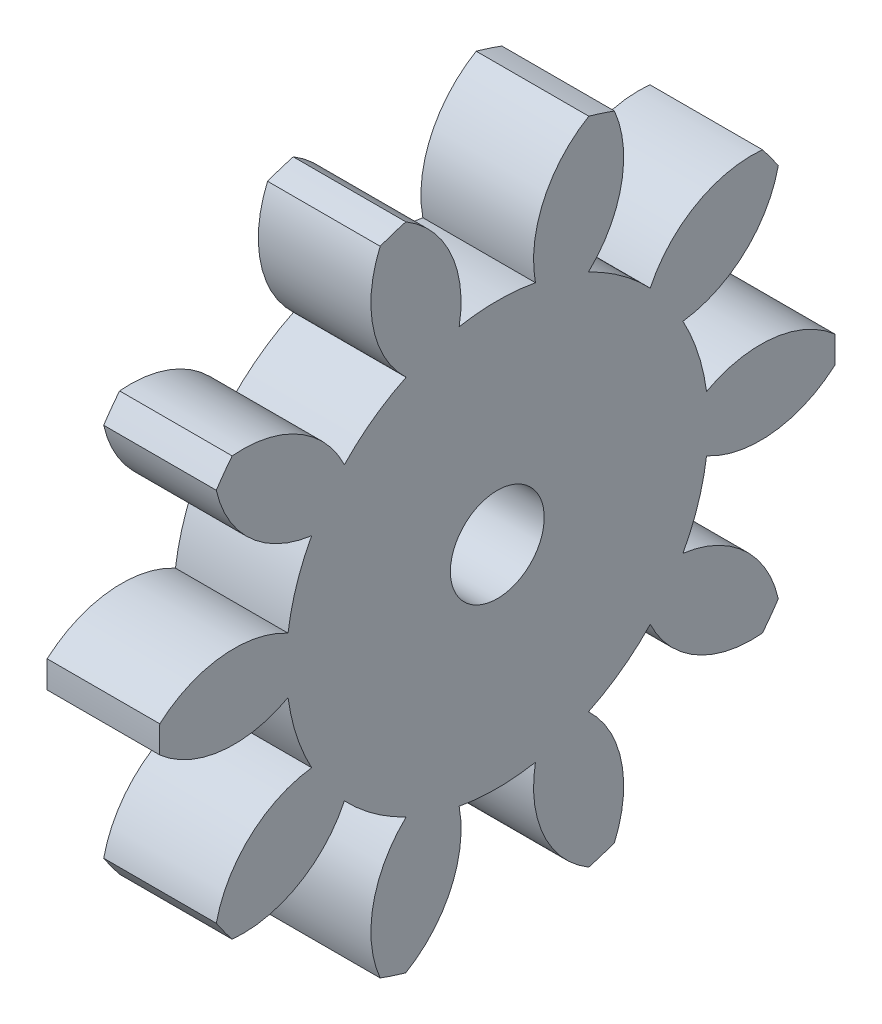
SolidWorks part; units mm, degrees
ref_plane "Plane1" through (0, 0, 0) normal (0, 0, 1) x (1, 0, 0)
ref_plane "Plane2" through (0, 0, 0) normal (0, 1, 0) x (1, 0, 0)
ref_plane "Plane3" through (0, 0, 0) normal (1, 0, 0) x (0, 0, -1)
other "Configuration Table"
sketch "HoldingSke" plane through (0, 0, 0) normal (0, 1, 0) x (1, 0, 0)
  line L0 (0, 0) -> (0.3283, -0.0579)
  line L1 (-15, 0) -> (100, 0) construction
  line L2 (0, 0) -> (-2.1039, 2.3779)
  line L3 (0, 0) -> (-11.863, 4.5341)
  line L4 (0, 0) -> (8.5048, 1.4996)
  line L5 (0, 0) -> (-46.8476, -17.4728)
  line L6 (0, 0) -> (-4.9738, -3.3558)
  line L7 (-2.1039, 2.3779) -> (8.6586, 51.2059)
  line L8 (-76.2, 54.61) -> (-75.3, 54.61)
  line L9 (-67.7845, 28.3722) -> (-49.3413, 33.142)
  line L10 (-76.2, 71.12) -> (104.1128, 71.12)
  line L11 (0, 0) -> (-6, 0)
  line L12 (-76.2, 101.6) -> (-76.093, 101.6)
  line L13 (24.9733, 27.94) -> (52.9518, 28.4284)
  line L14 (24.9733, 27.94) -> (24.9743, 27.94)
  line L15 (24.9733, 27.94) -> (100.4006, 29.5858)
  line L16 (-63.627, -3) -> (-12.827, -3)
  circle A0 centre (0, 0) radius 2.5
  circle A1 centre (0, 0) radius 11.249
  circle A2 centre (0, 0) radius 37.5
  circle A3 centre (0, 0) radius 2.5
  dimension "MHD" = 22.498
  dimension "Hub_dia" = 75
  dimension "Bore" = 5
  dimension "MBD" = 5
  dimension "Num_teeth" = 10
  dimension "Pitch" = 0.3333
  dimension "Overall_len" = 50
  dimension "Show_teeth" = 10
  dimension "Thickness" = 6
  dimension "OAL" = 50.0001
  dimension "T_dim" = 0.9
  dimension "Ap" = 14.5
  dimension "H" = 19.05
  dimension "Pitch_radius" = 180.3128
  dimension "Width" = 6
  dimension "Backlash" = 0.107
  dimension "Addendum_fac" = 1
  dimension "Dedendum_fac" = 1.25
  dimension "Clearance_fac" = 0.25
  dimension "Dedendum_add" = 0.001
  dimension "Module" = 3
sketch "BasProSke" plane through (0, 0, 0) normal (0, 1, 0) x (1, 0, 0)
  line L0 (-10, 0) -> (60, 0) construction
  line L1 (0, 0) -> (0, 18)
  line L2 (0, 0) -> (6, 0)
  line L3 (6, 0) -> (6, 18)
  line L4 (6, 18) -> (0, 18)
  dimension "Thickness" = 6
  dimension "Diameter" = 36
revolve "Base-Revolve" add sketch "BasProSke" angle 360 about L0
sketch "TooCutSke" plane through (0, 0, 0) normal (1, 0, 0) x (0, 0, -1)
  line L1 (0, 0) -> (0, 107) construction
  line L2 (0, 0) -> (-2.5334, 14.7845) construction
  line L3 (0, 0) -> (-9.174, 28.2345) construction
  line L4 (-2.5334, 14.7845) -> (-4.587, 14.1173) construction
  arc A0 (2.0333, 11.0637) -> (-2.0333, 11.0637) centre (0, 0) ccw
  arc A1 (4.9042, 17.3454) -> (-4.9042, 17.3454) centre (0, 0) ccw
  circle A2 centre (0, 0) radius 15 construction
  circle A3 centre (0, 0) radius 14.5222 construction
  arc A4 (-2.0333, 11.0637) -> (-4.9042, 17.3454) centre (-7.9314, 12.165) ccw
  arc A5 (4.9042, 17.3454) -> (2.0333, 11.0637) centre (7.9314, 12.165) ccw
  dimension "Root_dia" = 22.498
  dimension "Overcut_dia" = 36.0508
  dimension "Pitch_dia" = 30
  dimension "Base_dia" = 29.0444
  dimension "Flank_rad" = 6
  dimension "Half_ang" = 18
  dimension "Half_CT" = 2.1593
extrude "ToothCut" cut sketch "TooCutSke" along normal through all
fillet "Breaks" [suppressed] radius 0.06
fillet "RootFillets" [suppressed] radius 0.751
pattern_circular "TeethCuts" count 10 every 36 about axis through (-10, 0, 0) along (1, 0, 0) of "ToothCut", "RootFillets", "Breaks"
sketch "HubNeaOneSke" plane through (0, 0, 0) normal (-1, 0, 0) x (0, 0, 1)
  circle A0 centre (0, 0) radius 11.249
  dimension "Diameter" = 22.498
extrude "HubNearOne" [suppressed] add sketch "HubNeaOneSke" along normal blind 44.0001
sketch "HubNeaBotSke" plane through (0, 0, 0) normal (-1, 0, 0) x (0, 0, 1)
  circle A0 centre (0, 0) radius 11.249
  dimension "Diameter" = 22.498
extrude "HubNearBoth" [suppressed] add sketch "HubNeaBotSke" along normal blind 22
ref_plane "FarPln" through (6, 0, 0) normal (1, 0, 0) x (0, 0, -1)
sketch "HubFarSke" plane through (6, 0, 0) normal (1, 0, 0) x (0, 0, -1)
  circle A0 centre (0, 0) radius 11.249
  dimension "Diameter" = 22.498
extrude "HubFar" [suppressed] add sketch "HubFarSke" along normal blind 22
sketch "BorSke" plane through (0, 0, 0) normal (1, 0, 0) x (0, 0, -1)
  circle A0 centre (0, 0) radius 2.5
  dimension "Diameter" = 5
extrude "Bore" cut sketch "BorSke" along normal mid plane 100.0001
sketch "KeySke" plane through (0, 0, 0) normal (1, 0, 0) x (0, 0, -1)
  line L0 (-1, 0) -> (-1, 3.4)
  line L1 (-1, 3.4) -> (1, 3.4)
  line L2 (1, 3.4) -> (1, 0)
  line L3 (0, 0) -> (0, 34) construction
  line L4 (-1, 0) -> (1, 0)
  dimension "Offset" = 3.4
  dimension "Width" = 2
extrude "Keyway" [suppressed] cut sketch "KeySke" along normal mid plane 100.0001
pattern_circular "Keyway2" [suppressed] count 2 every 90 about axis through (-10, 0, 0) along (1, 0, 0)
equation "' \"Module@HoldingSke\" = 6.35"
equation "' \"Num_teeth@HoldingSke\" = 12"
equation "' \"Ap@HoldingSke\" =  20"
equation "' \"Ap@HoldingSke\" = 20"
equation "' \"Width@HoldingSke\" = 0.5 * 25.4"
equation "' \"Hub_dia@HoldingSke\"= 1 * 25.4"
equation "' \"Hub_dia@HoldingSke\" = 1 * 25.4"
equation "' \"Overall_len@HoldingSke\" = 1.0 * 25.4"
equation "' \"Bore@HoldingSke\" = 0.75 * 25.4"
equation "' \"T_dim@HoldingSke\" = 0.1 * 25.4"
equation "' \"Width@KeySke\" = 0.25 * 25.4"
equation "' \"Show_teeth@HoldingSke\" = 13"
equation "' \"Backlash@HoldingSke\" = 0.009 * 25.4"
equation "' \"Addendum_fac@HoldingSke\" = 1.0"
equation "' \"Dedendum_fac@HoldingSke\" = 1.25"
equation "' \"Dedendum_add@HoldingSke\" = 0.00005 * 25.4"
equation "' \"Clearance_fac@HoldingSke\" = 0.25"
equation "\"Pitch@HoldingSke\" = 1 / \"Module@HoldingSke\""
equation "\"Overcut_dia@TooCutSke\" = (\"Num_teeth@HoldingSke\" + 2 * \"Addendum_fac@HoldingSke\") / \"Pitch@HoldingSke\" + 0.002 * 25.4"
equation "\"Pitch_dia@TooCutSke\" = \"Num_teeth@HoldingSke\" / \"Pitch@HoldingSke\""
equation "\"Base_dia@TooCutSke\" = \"Num_teeth@HoldingSke\" / \"Pitch@HoldingSke\" * cos((\"Ap@HoldingSke\"  * 3.14159265 / 180))"
equation "\"Root_dia@TooCutSke\" = (\"Num_teeth@HoldingSke\" + 2) / \"Pitch@HoldingSke\" - 2 * (\"Addendum_fac@HoldingSke\" + \"Dedendum_fac@HoldingSke\") / \"Pitch@HoldingSke\" - \"Dedendum_add@HoldingSke\" * 2"
equation "\"Half_ang@TooCutSke\" = 180 / \"Num_teeth@HoldingSke\""
equation "\"Half_CT@TooCutSke\" = \"Num_teeth@HoldingSke\" / \"Pitch@HoldingSke\" * sin((3.14159265 / 2 / \"Num_teeth@HoldingSke\")) / 2 - 7 * \"Backlash@HoldingSke\" / 4"
equation "\"Flank_rad@TooCutSke\" = \"Num_teeth@HoldingSke\" / \"Pitch@HoldingSke\" / 5"
equation "\"Radius@RootFillets\" = \"Clearance_fac@HoldingSke\" / \"Pitch@HoldingSke\" + \"Dedendum_add@HoldingSke\""
equation "\"Break_rad@Breaks\" = 0.02 / \"Pitch@HoldingSke\""
equation "\"Thickness@HoldingSke\" = \"Width@HoldingSke\""
equation "\"OAL@HoldingSke\" = \"Thickness@HoldingSke\""
equation "\"MHD@HoldingSke\" = (\"Num_teeth@HoldingSke\" + 2) / \"Pitch@HoldingSke\" - 2 * (\"Addendum_fac@HoldingSke\" + \"Dedendum_fac@HoldingSke\")  / \"Pitch@HoldingSke\" - \"Dedendum_add@HoldingSke\" * 2"
equation "\"MBD@HoldingSke\" = (\"Num_teeth@HoldingSke\" + 2) / \"Pitch@HoldingSke\" - 2 * (\"Addendum_fac@HoldingSke\" + \"Dedendum_fac@HoldingSke\")  / \"Pitch@HoldingSke\" - \"Dedendum_add@HoldingSke\" * 2 - 0.002 * 25.4"
equation "\"MHD@HoldingSke\" = ((sgn( \"MHD@HoldingSke\" - \"Hub_dia@HoldingSke\" )-1)*( \"MHD@HoldingSke\" - \"Hub_dia@HoldingSke\" ))/-2+ \"Hub_dia@HoldingSke\""
equation "\"MBD@HoldingSke\" = ((sgn( \"MBD@HoldingSke\" - \"Bore@HoldingSke\" )-1)*( \"MBD@HoldingSke\" - \"Bore@HoldingSke\" ))/-2+ \"Bore@HoldingSke\""
equation "\"OAL@HoldingSke\" = ((sgn( \"OAL@HoldingSke\" - \"Overall_len@HoldingSke\" )+1)*( \"OAL@HoldingSke\" - \"Overall_len@HoldingSke\" ))/2 + \"Overall_len@HoldingSke\" + 0.000002 * 25.4"
equation "\"Num_teeth@TeethCuts\" = int( \"Show_teeth@HoldingSke\" ) + 1"
equation "\"Num_teeth@TeethCuts\" = ((sgn( \"Num_teeth@TeethCuts\" - \"Num_teeth@HoldingSke\" )-1)*( \"Num_teeth@TeethCuts\" - \"Num_teeth@HoldingSke\" ))/-2+ \"Num_teeth@HoldingSke\""
equation "\"Num_teeth@TeethCuts\" = ((sgn( \"Num_teeth@TeethCuts\" - 2.0)+1)*( \"Num_teeth@TeethCuts\" - 2.0))/2 +2.0"
equation "\"Angle@TeethCuts\" = 360.0 / \"Num_teeth@HoldingSke\""
equation "\"Diameter@BasProSke\" = (\"Num_teeth@HoldingSke\" + 2 * \"Addendum_fac@HoldingSke\") / \"Pitch@HoldingSke\""
equation "\"Thickness@BasProSke\"  = \"Thickness@HoldingSke\""
equation "' \"Fillet_rad@BasProSke\" =  \"Thickness@HoldingSke\" * 0.05"
equation "' \"Fillet_rad@BasProSke\" = \"Thickness@HoldingSke\" * 0.05"
equation "\"MHD@HoldingSke\" = ((sgn( \"MHD@HoldingSke\" - \"Root_dia@TooCutSke\" )-1)*( \"MHD@HoldingSke\" - \"Root_dia@TooCutSke\" ))/-2+ \"Root_dia@TooCutSke\""
equation "\"Diameter@HubNeaOneSke\" = \"MHD@HoldingSke\""
equation "\"Length@HubNearOne\" = \"OAL@HoldingSke\" - \"Thickness@BasProSke\""
equation "\"Diameter@HubNeaBotSke\" = \"MHD@HoldingSke\""
equation "\"Length@HubNearBoth\" = ( \"OAL@HoldingSke\" - \"Thickness@BasProSke\" ) / 2.0"
equation "\"Thickness@FarPln\" = \"Thickness@BasProSke\""
equation "\"Diameter@HubFarSke\" = \"MHD@HoldingSke\""
equation "\"Length@HubFar\" = ( \"OAL@HoldingSke\" - \"Thickness@BasProSke\" ) / 2.0"
equation "\"Diameter@BorSke\" = \"MBD@HoldingSke\""
equation "\"D1@Bore\" = \"OAL@HoldingSke\" * 2.0"
equation "\"D1@Keyway\" = \"OAL@HoldingSke\" * 2.0"
equation "\"Offset@KeySke\" = \"T_dim@HoldingSke\" + \"MBD@HoldingSke\" / 2.0"
